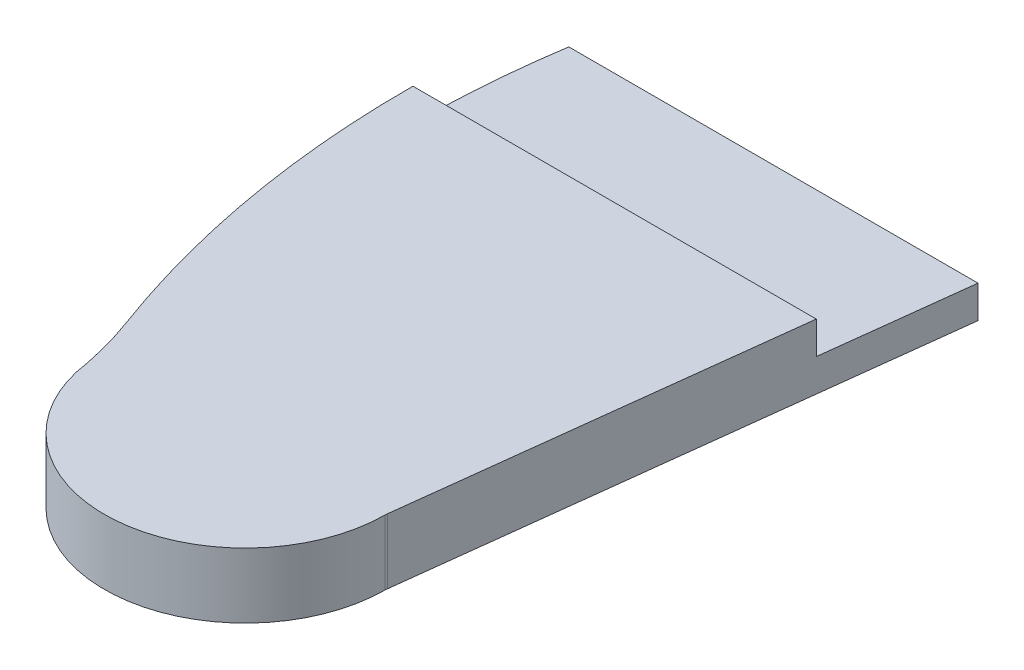
SolidWorks part; units mm, degrees
ref_plane "Plan de face" through (0, 0, 0) normal (0, 0, 1) x (1, 0, 0)
ref_plane "Plan de dessus" through (0, 0, 0) normal (0, 1, 0) x (1, 0, 0)
ref_plane "Plan de droite" through (0, 0, 0) normal (1, 0, 0) x (0, 0, -1)
sketch "Esquisse1" plane through (0, 0, 0) normal (0, 1, 0) x (1, 0, 0)
  line L0 (0, -574.2311) -> (0, 79.394) construction
  line L2 (140.9505, 96.5836) -> (140.9505, 49.2489) construction
  line L3 (176.9329, 42.7761) -> (130.0681, -349.4301)
  arc A0 (0.5762, -358.6356) -> (129.9978, -350.5343) centre (65, -350) ccw
  arc A1 (0.7929, 8.3134) -> (63.2851, 39.5132) centre (43.978, 0) cw
  arc A2 (176.9329, 42.7761) -> (104.297, 41.4996) centre (140.9193, 24.8199) ccw
  arc A3 (104.297, 41.4996) -> (63.2851, 39.5132) centre (84.6969, 21.8028) ccw
  arc A4 (-5.409, -13.622) -> (-6.3452, -333.8831) centre (420.8631, -175) ccw
  arc A5 (130.0681, -349.4301) -> (129.9978, -350.5343) centre (139.9975, -350.6165) ccw
  spline S0 degree 2 poles (0.7929, 8.3134) (-2.2098, -2.6814) (-5.409, -13.622) knots 0.221663 0.221663 0.221663 1 1 1
  spline S1 degree 2 poles (1.5587, -364.1491) (-1.0182, -348.0957) (-6.7573, -332.7704) knots 0 0 0 1 1 1
  point P23 (130, -350)
  dimension "D4" = 89.096
  dimension "D5" = 10
  dimension "D9" = 65
  dimension "D10" = 43.978
  dimension "D11" = 27.7872
  dimension "D12" = 40.2418
  dimension "D6" = 455.7969
  dimension "D7" = 36.5599
  dimension "D13" = 392.2062
  dimension "D14" = 41.0601
  dimension "D15" = 72.6358
extrude "Boss.-Extru.7" add sketch "Esquisse1" along normal blind 30
ref_plane "Plan2" through (580.7158, 0, 0) normal (1, 0, 0) x (0, 0, -1)
scale "Echelle1" scale about centroid uniform scaling yes scale factor 0.45
sketch "Esquisse2" plane through (0, 0, 0) normal (0, 1, 0) x (1, 0, 0)
  line L1 (123.9791, -138.392) -> (18.3163, -138.392)
  line L2 (123.9791, -138.392) -> (123.9791, -28.392)
  line L3 (123.9791, -28.392) -> (18.3163, -28.392)
  line L4 (18.3163, -138.392) -> (18.3163, -28.392)
  arc A0 (84.153, -72.018) -> (65.6976, -72.9119) centre (75.333, -80.8816) ccw construction
  point P4 (74.7281, -68.392)
  dimension "D1" = 105.6628
  dimension "D2" = 70
  dimension "D3" = 110
extrude "Enlèv. mat.-Extru.1" cut sketch "Esquisse2" along normal through all
sketch "Esquisse3" plane through (580.7158, 0, 0) normal (1, 0, 0) x (0, 0, -1)
  line L1 (-168.392, 15) -> (-138.392, 15)
  line L2 (-168.392, 15) -> (-168.392, 21.75)
  line L3 (-168.392, 21.75) -> (-138.392, 21.75)
  line L4 (-138.392, 15) -> (-138.392, 21.75)
  dimension "D1" = 6.75
  dimension "D2" = 30
extrude "Enlèv. mat.-Extru.3" cut sketch "Esquisse3" against normal through all
